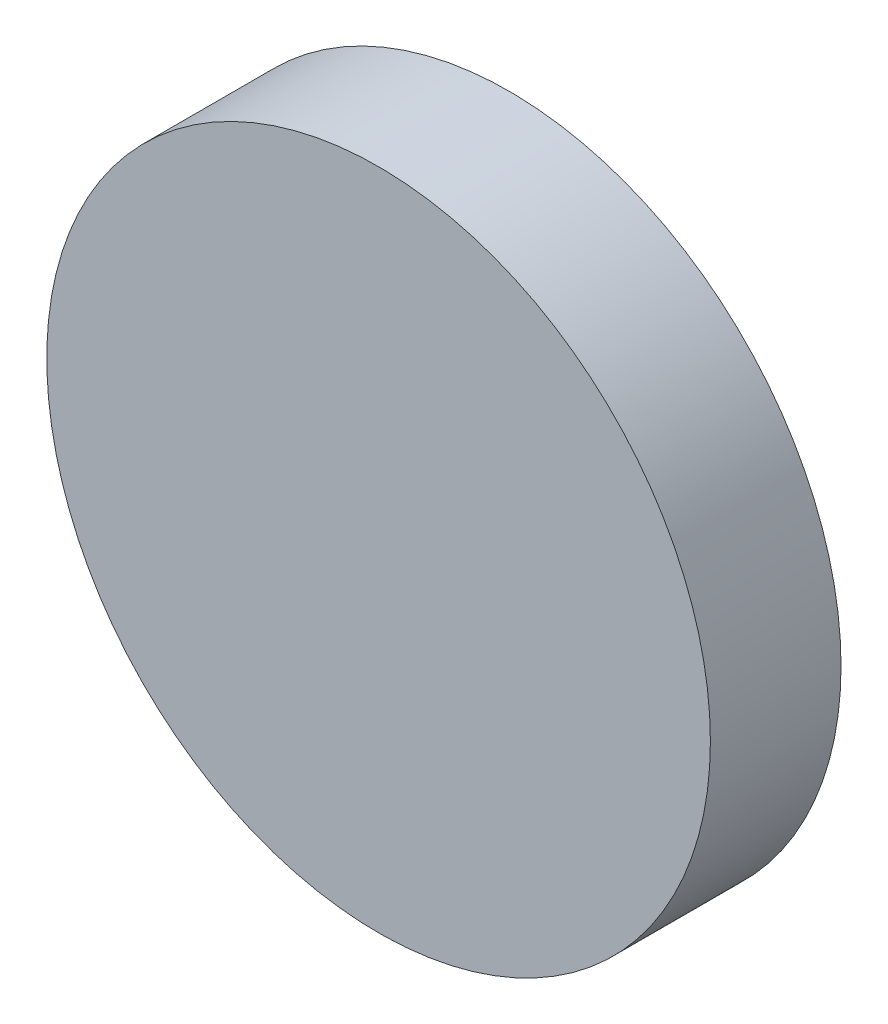
SolidWorks part; units mm, degrees
ref_plane "Front Plane" through (0, 0, 0) normal (0, 0, 1) x (1, 0, 0)
ref_plane "Top Plane" through (0, 0, 0) normal (0, 1, 0) x (1, 0, 0)
ref_plane "Right Plane" through (0, 0, 0) normal (1, 0, 0) x (0, 0, -1)
sketch "Sketch1" plane through (0, 0, 0) normal (0, 0, 1) x (1, 0, 0)
  circle A0 centre (0, 0) radius 20
  dimension "D1" = 40
extrude "Boss-Extrude1" add sketch "Sketch1" along normal blind 7.874
